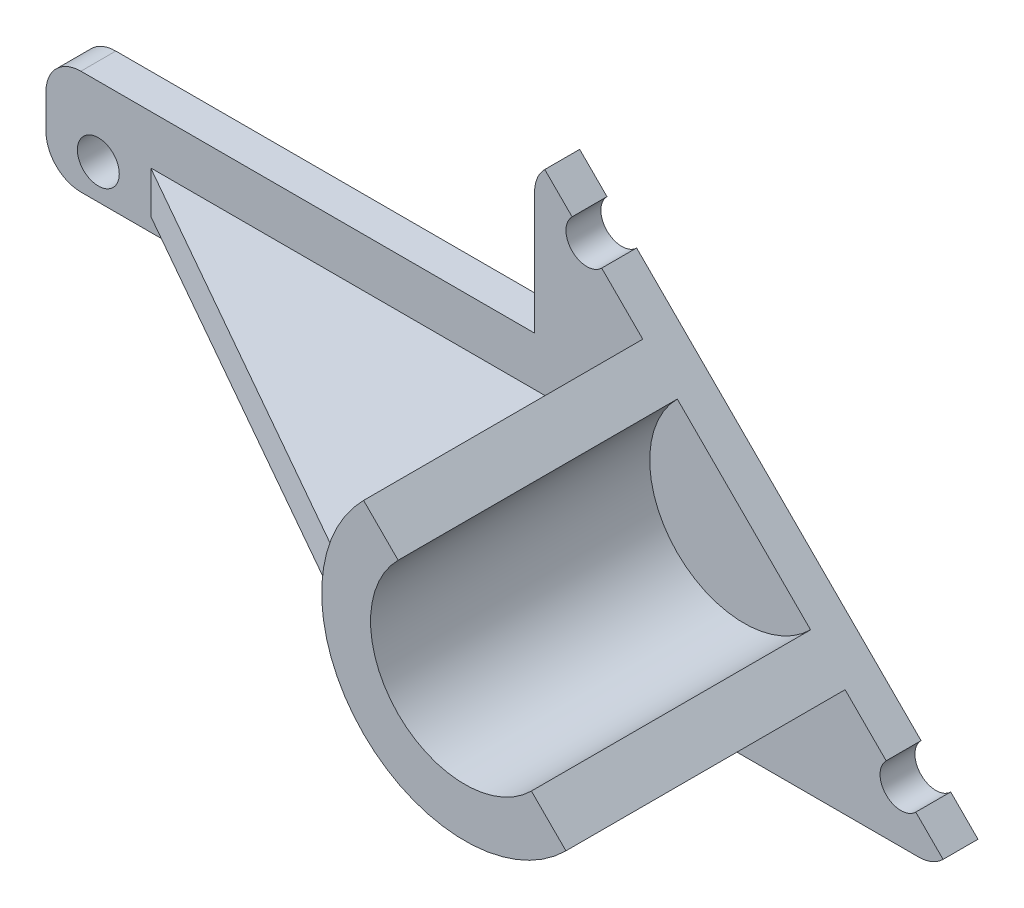
SolidWorks part; units mm, degrees
ref_plane "Alzado" through (0, 0, 0) normal (0, 0, 1) x (1, 0, 0)
ref_plane "Planta" through (0, 0, 0) normal (0, 1, 0) x (1, 0, 0)
ref_plane "Vista lateral" through (0, 0, 0) normal (1, 0, 0) x (0, 0, -1)
sketch "Croquis1" plane through (0, 0, 0) normal (0, 0, 1) x (1, 0, 0)
  line L0 (-25, 16.3171) -> (-95, 16.3171)
  line L1 (-25, -21.1829) -> (30, -21.1829)
  line L2 (-25, -21.1829) -> (-25, 1.3171)
  line L5 (-25, -21.1829) -> (25, 26.1829) construction
  line L6 (-25, 38.8171) -> (35, -21.1829) construction
  line L7 (-95, 16.3171) -> (-95, 1.3171)
  line L8 (-95, 1.3171) -> (-25, 1.3171)
  line L9 (-23.5355, 37.3526) -> (33.5355, -19.7184)
  line L10 (-25, 16.3171) -> (-25, 33.8171)
  arc A0 (-23.5355, 37.3526) -> (-25, 33.8171) centre (-20, 33.8171) ccw
  arc A1 (30, -21.1829) -> (33.5355, -19.7184) centre (30, -16.1829) ccw
  dimension "D6" = 10
  dimension "D7" = 10
  dimension "D1" = 60
  dimension "D2" = 60
  dimension "D3" = 15
  dimension "D4" = 22.5
  dimension "D5" = 70
  dimension "D8" = 42.4264
extrude "Saliente-Extruir1" add sketch "Croquis1" along normal blind 5
sketch "Croquis2" plane through (0, 0, 5) normal (0, 0, 1) x (1, 0, 0)
  line L1 (-9.4957, 23.3128) -> (-4.5459, 18.363)
  line L2 (14.5459, -0.7288) -> (19.4957, -5.6786)
  line L3 (33.5355, -19.7184) -> (-23.5355, 37.3526) construction
  arc A0 (-9.4957, 23.3128) -> (19.4957, -5.6786) centre (5, 8.8171) ccw
  arc A1 (-4.5459, 18.363) -> (14.5459, -0.7288) centre (5, 8.8171) ccw
  line M3 (33.5355, -19.7184) -> (-23.5355, 37.3526)
  dimension "D1" = 27
  dimension "D2" = 41
extrude "Saliente-Extruir2" add sketch "Croquis2" along normal blind 40 contours A1 A0 M3
sketch "Croquis4" plane through (0, 0, 5) normal (0, 0, 1) x (1, 0, 0)
  line L0 (-80, 16.3171) -> (-80, 1.3171) construction
  line L1 (-25, 16.3171) -> (-95, 16.3171) construction
  line L2 (-95, 1.3171) -> (-25, 1.3171) construction
  line L3 (-95, 16.3171) -> (-95, 1.3171) construction
  dimension "D1" = 15
ref_plane "Plano2" through (-21.6259, 0, 38.118) normal (-0.4935, 0, 0.8698) x (0.8698, 0, 0.4935)
sketch "Croquis5" plane through (-21.6259, 0, 38.118) normal (-0.4935, 0, 0.8698) x (0.8698, 0, 0.4935)
  line L1 (-66.9682, 6.3171) -> (8.4625, 6.3171)
extrude "Extruir-Lámina2" add sketch "Croquis5" against normal up to next thin thin type mid plane wall 6
fillet "Redondeo1" radius 5 3 edges at (-25, -21.1829, 2.5) (-95, 16.3171, 2.5) (-95, 1.3171, 2.5)
sketch "Croquis6" plane through (0, 0, 5) normal (0, 0, 1) x (1, 0, 0)
  line L0 (35, -21.1829) -> (-25, 38.8171) construction
  line L1 (-95, 11.3171) -> (-95, 6.3171) construction
  line L3 (-25, 33.8171) -> (-25, 16.3171) construction
  line L4 (-20, -21.1829) -> (30, -21.1829) construction
  line L5 (-25, 1.3171) -> (-25, -16.1829) construction
  circle A0 centre (-87.5, 6.3171) radius 3
  circle A1 centre (-17.5, -13.6829) radius 3
  circle A2 centre (-17.5, 31.3171) radius 3
  circle A3 centre (27.5, -13.6829) radius 3
  dimension "D1" = 6
  dimension "D2" = 6
  dimension "D3" = 6
  dimension "D4" = 6
  dimension "D5" = 7.5
  dimension "D6" = 7.5
  dimension "D7" = 7.5
  dimension "D8" = 7.5
  dimension "D9" = 7.5
extrude "Cortar-Extruir1" cut sketch "Croquis6" against normal blind 40
